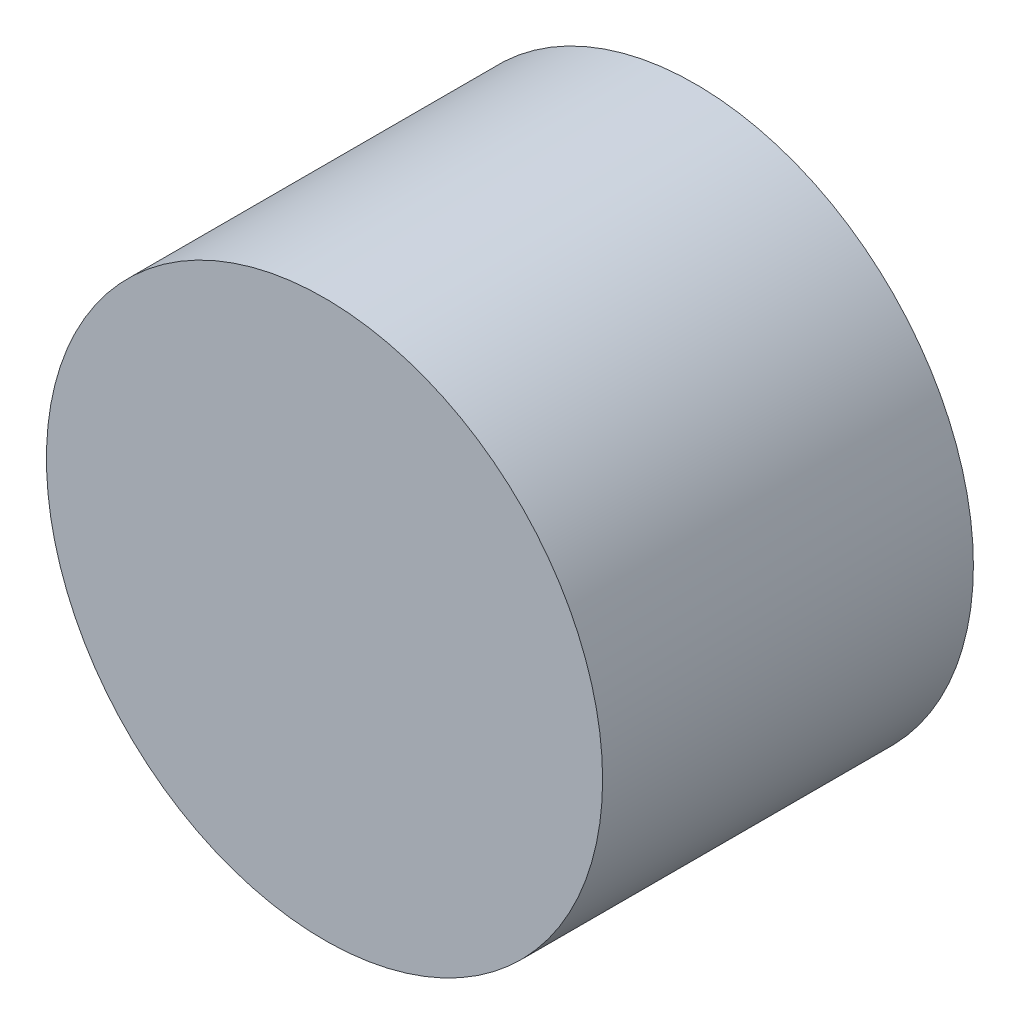
SolidWorks part; units mm, degrees
ref_plane "Face" through (0, 0, 0) normal (0, 0, 1) x (1, 0, 0)
ref_plane "Dessus" through (0, 0, 0) normal (0, 1, 0) x (1, 0, 0)
ref_plane "Droite" through (0, 0, 0) normal (1, 0, 0) x (0, 0, -1)
sketch "Esquisse1" plane through (0, 0, 0) normal (0, 0, 1) x (1, 0, 0)
  circle A0 centre (0, 0) radius 1.5
  dimension "D1" = 3
extrude "Extrusion1" add sketch "Esquisse1" along normal blind 2
